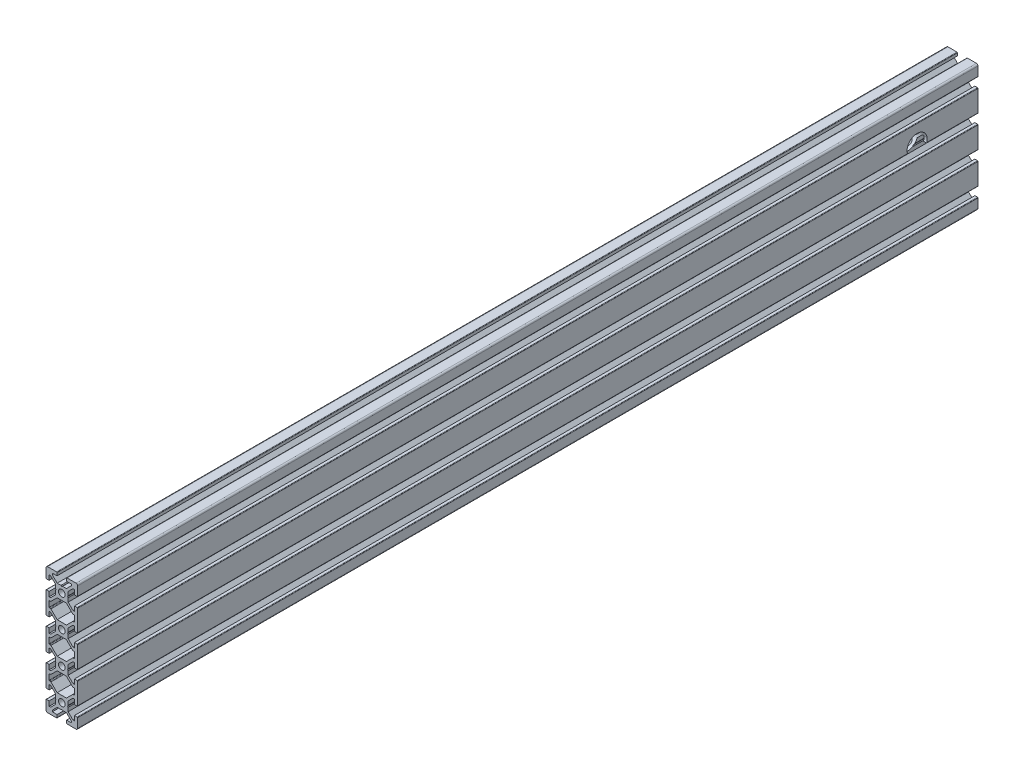
SolidWorks part; units mm, degrees
material "6063-T5"
ref_plane "Front Plane" through (0, 0, 0) normal (0, 0, 1) x (1, 0, 0)
ref_plane "Top Plane" through (0, 0, 0) normal (0, 1, 0) x (1, 0, 0)
ref_plane "Right Plane" through (0, 0, 0) normal (1, 0, 0) x (0, 0, -1)
ref_plane "Plane1" through (0, 0, 0) normal (0, 0, 1) x (1, 0, 0)
sketch "Sketch1" plane through (0, 0, 0) normal (0, 0, 1) x (1, 0, 0)
  line L0 (-9.7, -7) -> (-8, -7)
  line L1 (-8, -7) -> (-8, -4)
  line L2 (-8, -4) -> (-7.0606, -4)
  line L3 (-7.0606, -4) -> (-4, -7.0606)
  line L4 (-4, -7.0606) -> (-4, -9.4804)
  line L5 (-4, -9.4804) -> (-3.7, -10)
  line L6 (-3.7, -10) -> (-4, -10.5196)
  line L7 (-4, -10.5196) -> (-4, -12.9393)
  line L8 (-4, -12.9393) -> (-7.0607, -16)
  line L9 (-7.0607, -16) -> (-8, -16)
  line L10 (-8, -16) -> (-8, -13)
  line L11 (-8, -13) -> (-9.7, -13)
  line L12 (-10, -13.3) -> (-10, -26.7)
  line L13 (-9.7, -27) -> (-8, -27)
  line L14 (-8, -27) -> (-8, -24)
  line L15 (-8, -24) -> (-7.0606, -24)
  line L16 (-7.0606, -24) -> (-4, -27.0606)
  line L17 (-4, -27.0606) -> (-4, -29.4804)
  line L18 (-4, -29.4804) -> (-3.7, -30)
  line L19 (-3.7, -30) -> (-4, -30.5196)
  line L20 (-4, -30.5196) -> (-4, -32.9393)
  line L21 (-4, -32.9393) -> (-7.0607, -36)
  line L22 (-7.0607, -36) -> (-8, -36)
  line L23 (-8, -36) -> (-8, -33)
  line L24 (-8, -33) -> (-9.7, -33)
  line L25 (-10, -33.3) -> (-10, -39)
  line L26 (-9, -40) -> (-3.3, -40)
  line L27 (-3, -39.7) -> (-3, -38)
  line L28 (-3, -38) -> (-6, -38)
  line L29 (-6, -38) -> (-6, -37.0607)
  line L30 (-6, -37.0607) -> (-2.9393, -34)
  line L31 (-2.9393, -34) -> (-0.5196, -34)
  line L32 (-0.5196, -34) -> (0, -33.7)
  line L33 (0, -33.7) -> (0.5196, -34)
  line L34 (0.5196, -34) -> (2.9393, -34)
  line L35 (2.9393, -34) -> (6, -37.0607)
  line L36 (6, -37.0607) -> (6, -38)
  line L37 (6, -38) -> (3, -38)
  line L38 (3, -38) -> (3, -39.7)
  line L39 (3.3, -40) -> (9, -40)
  line L40 (10, -39) -> (10, -33.3)
  line L41 (9.7, -33) -> (8, -33)
  line L42 (8, -33) -> (8, -36)
  line L43 (8, -36) -> (7.0607, -36)
  line L44 (7.0607, -36) -> (4, -32.9393)
  line L45 (4, -32.9393) -> (4, -30.5196)
  line L46 (4, -30.5196) -> (3.7, -30)
  line L47 (3.7, -30) -> (4, -29.4804)
  line L48 (4, -29.4804) -> (4, -27.0606)
  line L49 (4, -27.0606) -> (7.0606, -24)
  line L50 (7.0606, -24) -> (8, -24)
  line L51 (8, -24) -> (8, -27)
  line L52 (8, -27) -> (9.7, -27)
  line L53 (10, -26.7) -> (10, -13.3)
  line L54 (9.7, -13) -> (8, -13)
  line L55 (8, -13) -> (8, -16)
  line L56 (8, -16) -> (7.0607, -16)
  line L57 (7.0607, -16) -> (4, -12.9393)
  line L58 (4, -12.9393) -> (4, -10.5196)
  line L59 (4, -10.5196) -> (3.7, -10)
  line L60 (3.7, -10) -> (4, -9.4804)
  line L61 (4, -9.4804) -> (4, -7.0606)
  line L62 (4, -7.0606) -> (7.0606, -4)
  line L63 (7.0606, -4) -> (8, -4)
  line L64 (8, -4) -> (8, -7)
  line L65 (8, -7) -> (9.7, -7)
  line L66 (10, -6.7) -> (10, 6.7)
  line L67 (9.7, 7) -> (8, 7)
  line L68 (8, 7) -> (8, 4)
  line L69 (8, 4) -> (7.0606, 4)
  line L70 (7.0606, 4) -> (4, 7.0606)
  line L71 (4, 7.0606) -> (4, 9.4804)
  line L72 (4, 9.4804) -> (3.7, 10)
  line L73 (3.7, 10) -> (4, 10.5196)
  line L74 (4, 10.5196) -> (4, 12.9393)
  line L75 (4, 12.9393) -> (7.0607, 16)
  line L76 (7.0607, 16) -> (8, 16)
  line L77 (8, 16) -> (8, 13)
  line L78 (8, 13) -> (9.7, 13)
  line L79 (10, 13.3) -> (10, 26.7)
  line L80 (9.7, 27) -> (8, 27)
  line L81 (8, 27) -> (8, 24)
  line L82 (8, 24) -> (7.0606, 24)
  line L83 (7.0606, 24) -> (4, 27.0606)
  line L84 (4, 27.0606) -> (4, 29.4804)
  line L85 (4, 29.4804) -> (3.7, 30)
  line L86 (3.7, 30) -> (4, 30.5196)
  line L87 (4, 30.5196) -> (4, 32.9393)
  line L88 (4, 32.9393) -> (7.0607, 36)
  line L89 (7.0607, 36) -> (8, 36)
  line L90 (8, 36) -> (8, 33)
  line L91 (8, 33) -> (9.7, 33)
  line L92 (10, 33.3) -> (10, 39)
  line L93 (9, 40) -> (3.3, 40)
  line L94 (3, 39.7) -> (3, 38)
  line L95 (3, 38) -> (6, 38)
  line L96 (6, 38) -> (6, 37.0607)
  line L97 (6, 37.0607) -> (2.9393, 34)
  line L98 (2.9393, 34) -> (0.5196, 34)
  line L99 (0.5196, 34) -> (0, 33.7)
  line L100 (0, 33.7) -> (-0.5196, 34)
  line L101 (-0.5196, 34) -> (-2.9393, 34)
  line L102 (-2.9393, 34) -> (-6, 37.0607)
  line L103 (-6, 37.0607) -> (-6, 38)
  line L104 (-6, 38) -> (-3, 38)
  line L105 (-3, 38) -> (-3, 39.7)
  line L106 (-3.3, 40) -> (-9, 40)
  line L107 (-10, 39) -> (-10, 33.3)
  line L108 (-9.7, 33) -> (-8, 33)
  line L109 (-8, 33) -> (-8, 36)
  line L110 (-8, 36) -> (-7.0607, 36)
  line L111 (-7.0607, 36) -> (-4, 32.9393)
  line L112 (-4, 32.9393) -> (-4, 30.5196)
  line L113 (-4, 30.5196) -> (-3.7, 30)
  line L114 (-3.7, 30) -> (-4, 29.4804)
  line L115 (-4, 29.4804) -> (-4, 27.0606)
  line L116 (-4, 27.0606) -> (-7.0606, 24)
  line L117 (-7.0606, 24) -> (-8, 24)
  line L118 (-8, 24) -> (-8, 27)
  line L119 (-8, 27) -> (-9.7, 27)
  line L120 (-10, 26.7) -> (-10, 13.3)
  line L121 (-9.7, 13) -> (-8, 13)
  line L122 (-8, 13) -> (-8, 16)
  line L123 (-8, 16) -> (-7.0607, 16)
  line L124 (-7.0607, 16) -> (-4, 12.9393)
  line L125 (-4, 12.9393) -> (-4, 10.5196)
  line L126 (-4, 10.5196) -> (-3.7, 10)
  line L127 (-3.7, 10) -> (-4, 9.4804)
  line L128 (-4, 9.4804) -> (-4, 7.0606)
  line L129 (-4, 7.0606) -> (-7.0606, 4)
  line L130 (-7.0606, 4) -> (-8, 4)
  line L131 (-8, 4) -> (-8, 7)
  line L132 (-8, 7) -> (-9.7, 7)
  line L133 (-10, 6.7) -> (-10, -6.7)
  line L134 (-7.7, -2) -> (-7.0636, -2)
  line L135 (-6.8515, -2.0878) -> (-2.9393, -6)
  line L136 (-2.9393, -6) -> (2.9393, -6)
  line L137 (2.9393, -6) -> (6.8515, -2.0878)
  line L138 (7.0636, -2) -> (7.7, -2)
  line L139 (8, -1.7) -> (8, 1.7)
  line L140 (7.7, 2) -> (7.0636, 2)
  line L141 (6.8515, 2.0878) -> (2.9393, 6)
  line L142 (2.9393, 6) -> (-2.9393, 6)
  line L143 (-2.9393, 6) -> (-6.8515, 2.0878)
  line L144 (-7.0636, 2) -> (-7.7, 2)
  line L145 (-8, 1.7) -> (-8, -1.7)
  line L146 (-8, 21.7) -> (-8, 18.2999)
  line L147 (-7.7, 18) -> (-7.0636, 18)
  line L148 (-6.8515, 17.9121) -> (-2.9394, 14)
  line L149 (-2.9394, 14) -> (2.9394, 14)
  line L150 (2.9394, 14) -> (6.8515, 17.9121)
  line L151 (7.0636, 18) -> (7.7, 18)
  line L152 (8, 18.2999) -> (8, 21.7)
  line L153 (7.7, 22) -> (7.0636, 22)
  line L154 (6.8515, 22.0878) -> (2.9393, 26)
  line L155 (2.9393, 26) -> (-2.9393, 26)
  line L156 (-2.9393, 26) -> (-6.8515, 22.0878)
  line L157 (-7.0636, 22) -> (-7.7, 22)
  line L158 (-8, -18.2999) -> (-8, -21.7)
  line L159 (-7.7, -22) -> (-7.0636, -22)
  line L160 (-6.8515, -22.0878) -> (-2.9393, -26)
  line L161 (-2.9393, -26) -> (2.9393, -26)
  line L162 (2.9393, -26) -> (6.8515, -22.0878)
  line L163 (7.0636, -22) -> (7.7, -22)
  line L164 (8, -21.7) -> (8, -18.2999)
  line L165 (7.7, -18) -> (7.0636, -18)
  line L166 (6.8515, -17.9121) -> (2.9394, -14)
  line L167 (2.9394, -14) -> (-2.9394, -14)
  line L168 (-2.9394, -14) -> (-6.8515, -17.9121)
  line L169 (-7.0636, -18) -> (-7.7, -18)
  arc A0 (-10, -6.7) -> (-9.7, -7) centre (-9.7, -6.7) ccw
  arc A1 (-9.7, -13) -> (-10, -13.3) centre (-9.7, -13.3) ccw
  arc A2 (-10, -26.7) -> (-9.7, -27) centre (-9.7, -26.7) ccw
  arc A3 (-9.7, -33) -> (-10, -33.3) centre (-9.7, -33.3) ccw
  arc A4 (-10, -39) -> (-9, -40) centre (-9, -39) ccw
  arc A5 (-3.3, -40) -> (-3, -39.7) centre (-3.3, -39.7) ccw
  arc A6 (3, -39.7) -> (3.3, -40) centre (3.3, -39.7) ccw
  arc A7 (9, -40) -> (10, -39) centre (9, -39) ccw
  arc A8 (10, -33.3) -> (9.7, -33) centre (9.7, -33.3) ccw
  arc A9 (9.7, -27) -> (10, -26.7) centre (9.7, -26.7) ccw
  arc A10 (10, -13.3) -> (9.7, -13) centre (9.7, -13.3) ccw
  arc A11 (9.7, -7) -> (10, -6.7) centre (9.7, -6.7) ccw
  arc A12 (10, 6.7) -> (9.7, 7) centre (9.7, 6.7) ccw
  arc A13 (9.7, 13) -> (10, 13.3) centre (9.7, 13.3) ccw
  arc A14 (10, 26.7) -> (9.7, 27) centre (9.7, 26.7) ccw
  arc A15 (9.7, 33) -> (10, 33.3) centre (9.7, 33.3) ccw
  arc A16 (10, 39) -> (9, 40) centre (9, 39) ccw
  arc A17 (3.3, 40) -> (3, 39.7) centre (3.3, 39.7) ccw
  arc A18 (-3, 39.7) -> (-3.3, 40) centre (-3.3, 39.7) ccw
  arc A19 (-9, 40) -> (-10, 39) centre (-9, 39) ccw
  arc A20 (-10, 33.3) -> (-9.7, 33) centre (-9.7, 33.3) ccw
  arc A21 (-9.7, 27) -> (-10, 26.7) centre (-9.7, 26.7) ccw
  arc A22 (-10, 13.3) -> (-9.7, 13) centre (-9.7, 13.3) ccw
  arc A23 (-9.7, 7) -> (-10, 6.7) centre (-9.7, 6.7) ccw
  circle A24 centre (0, 30) radius 2.1
  circle A25 centre (0, 10) radius 2.1
  circle A26 centre (0, -10) radius 2.1
  circle A27 centre (0, -30) radius 2.1
  arc A28 (-8, -1.7) -> (-7.7, -2) centre (-7.7, -1.7) ccw
  arc A29 (-7.0636, -2) -> (-6.8515, -2.0878) centre (-7.0633, -2.2994) cw
  arc A30 (6.8515, -2.0878) -> (7.0636, -2) centre (7.0633, -2.2994) cw
  arc A31 (7.7, -2) -> (8, -1.7) centre (7.7, -1.7) ccw
  arc A32 (8, 1.7) -> (7.7, 2) centre (7.7, 1.7) ccw
  arc A33 (7.0636, 2) -> (6.8515, 2.0878) centre (7.0633, 2.2994) cw
  arc A34 (-6.8515, 2.0878) -> (-7.0636, 2) centre (-7.0633, 2.2994) cw
  arc A35 (-7.7, 2) -> (-8, 1.7) centre (-7.7, 1.7) ccw
  arc A36 (-8, 18.2999) -> (-7.7, 18) centre (-7.7001, 18.2999) ccw
  arc A37 (-7.0636, 18) -> (-6.8515, 17.9121) centre (-7.0638, 17.6996) cw
  arc A38 (6.8515, 17.9121) -> (7.0636, 18) centre (7.0638, 17.6996) cw
  arc A39 (7.7, 18) -> (8, 18.2999) centre (7.7001, 18.2999) ccw
  arc A40 (8, 21.7) -> (7.7, 22) centre (7.6999, 21.6999) ccw
  arc A41 (7.0636, 22) -> (6.8515, 22.0878) centre (7.0633, 22.2993) cw
  arc A42 (-6.8515, 22.0878) -> (-7.0636, 22) centre (-7.0633, 22.2993) cw
  arc A43 (-7.7, 22) -> (-8, 21.7) centre (-7.6999, 21.6999) ccw
  arc A44 (-8, -21.7) -> (-7.7, -22) centre (-7.6999, -21.6999) ccw
  arc A45 (-7.0636, -22) -> (-6.8515, -22.0878) centre (-7.0633, -22.2993) cw
  arc A46 (6.8515, -22.0878) -> (7.0636, -22) centre (7.0633, -22.2993) cw
  arc A47 (7.7, -22) -> (8, -21.7) centre (7.6999, -21.6999) ccw
  arc A48 (8, -18.2999) -> (7.7, -18) centre (7.7001, -18.2999) ccw
  arc A49 (7.0636, -18) -> (6.8515, -17.9121) centre (7.0638, -17.6996) cw
  arc A50 (-6.8515, -17.9121) -> (-7.0636, -18) centre (-7.0638, -17.6996) cw
  arc A51 (-7.7, -18) -> (-8, -18.2999) centre (-7.7001, -18.2999) ccw
extrude "Boss-Extrude1" add sketch "Sketch1" against normal blind 569.5
sketch "Sketch2" plane through (10, 0, 0) normal (1, 0, 0) x (0, 0, -1)
  line L0 (569.5, 13.3) -> (569.5, 26.7) construction
  line L1 (569.5, 40) -> (0, 40) construction
  circle A0 centre (531, 15) radius 6.35
  dimension "D1" = 38.5
  dimension "D2" = 25
  dimension "D3" = 12.7
extrude "Cut-Extrude1" cut sketch "Sketch2" against normal up to surface (20 mm away) up to face at (-10, 20, -284.75)
sketch "Sketch3" [suppressed] plane through (10, 0, 0) normal (1, 0, 0) x (0, 0, -1)
  line L0 (569.5, 40) -> (0, 40) construction
  line L1 (0, 13.3) -> (0, 26.7) construction
  circle A0 centre (38.5, 15) radius 6.35
  dimension "D1" = 25
  dimension "D2" = 38.5
  dimension "D3" = 12.7
extrude "Cut-Extrude2" [suppressed] cut sketch "Sketch3" against normal up to surface (20 mm away)
sketch "Sketch4" [suppressed] plane through (10, 0, 0) normal (1, 0, 0) x (0, 0, -1)
  line L0 (284.75, 40) -> (284.75, -40) construction
  line L1 (569.5, 40) -> (0, 40) construction
  line L2 (569.5, -40) -> (0, -40) construction
  line L3 (0, -6.7) -> (0, 6.7) construction
  line L4 (0, -26.7) -> (0, -13.3) construction
  circle A0 centre (38.5, -5) radius 6.35
  circle A1 centre (531, -5) radius 6.35
  circle A2 centre (225, -30) radius 2.5
  circle A3 centre (245, -30) radius 2.5
  circle A4 centre (265, -30) radius 2.5
  circle A5 centre (285, -30) radius 2.5
  dimension "D1" = 12.7
  dimension "D2" = 45
  dimension "D3" = 38.5
  dimension "D4" = 5
  dimension "D5" = 10
  dimension "D6" = 225
  dimension "D8" = 20
  dimension "D7" = 4
extrude "Cut-Extrude3" [suppressed] cut sketch "Sketch4" against normal up to surface (20 mm away)
sketch "Sketch5" [suppressed] plane through (10, 0, 0) normal (1, 0, 0) x (0, 0, -1)
  line L0 (0, 13.3) -> (0, 26.7) construction
  line L1 (569.5, 40) -> (0, 40) construction
  circle A0 centre (225, 30) radius 2.5
  circle A1 centre (245, 30) radius 2.5
  circle A2 centre (265, 30) radius 2.5
  circle A3 centre (285, 30) radius 2.5
  circle A4 centre (225, 10) radius 2.5
  circle A5 centre (245, 10) radius 2.5
  circle A6 centre (265, 10) radius 2.5
  circle A7 centre (285, 10) radius 2.5
  dimension "D1" = 5
  dimension "D2" = 225
  dimension "D3" = 10
  dimension "D5" = 20
  dimension "D7" = 20
  dimension "D4" = 4
  dimension "D6" = 2
extrude "Cut-Extrude4" [suppressed] cut sketch "Sketch5" against normal up to surface (20 mm away)
sketch "Sketch6" [suppressed] plane through (10, 0, 0) normal (1, 0, 0) x (0, 0, -1)
  line L0 (569.5, -40) -> (0, -40) construction
  line L1 (0, -26.7) -> (0, -13.3) construction
  circle A0 centre (225, -30) radius 2.5
  circle A1 centre (245, -30) radius 2.5
  circle A2 centre (265, -30) radius 2.5
  circle A3 centre (285, -30) radius 2.5
  dimension "D1" = 5
  dimension "D2" = 10
  dimension "D3" = 225
  dimension "D5" = 20
  dimension "D4" = 4
extrude "Cut-Extrude5" [suppressed] cut sketch "Sketch6" against normal up to surface (20 mm away)
